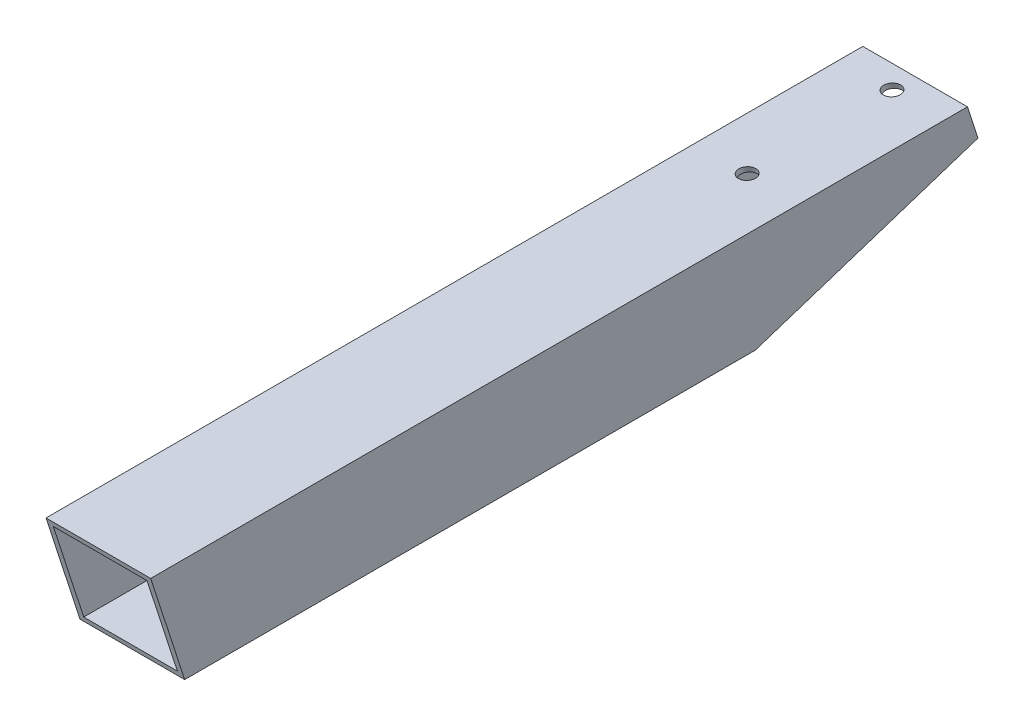
SolidWorks part; units mm, degrees
material "Gerais  - 6061-T6"
ref_plane "Plano frontal" through (0, 0, 0) normal (0, 0, 1) x (1, 0, 0)
ref_plane "Plano superior" through (0, 0, 0) normal (0, 1, 0) x (1, 0, 0)
ref_plane "Plano direito" through (0, 0, 0) normal (1, 0, 0) x (0, 0, -1)
sketch "Esboço1" plane through (0, 0, 0) normal (0, 0, 1) x (1, 0, 0)
  line L1 (-9.5, 9.5) -> (9.5, 9.5)
  line L2 (-9.5, 9.5) -> (-9.5, -9.5)
  line L3 (-9.5, -9.5) -> (9.5, -9.5)
  line L4 (9.5, 9.5) -> (9.5, -9.5)
  line L5 (-9.5, 9.5) -> (9.5, -9.5) construction
  line L6 (-9.5, -9.5) -> (9.5, 9.5) construction
  line L11 (-5.6574, 5.6574) -> (5.6574, -5.6574) construction
  line L12 (-5.6574, -5.6574) -> (5.6574, 5.6574) construction
  point P0 (0, 0)
  point P6 (0, 0)
  dimension "D1" = 19
extrude "Ressalto-extrusão1" add sketch "Esboço1" along normal blind 260
shell "Casca2" thickness 1
sketch "Esboço2" plane through (9.5, 0, 0) normal (1, 0, 0) x (0, 0, -1)
  line L0 (0, 9.5) -> (-58.476, -9.5)
  line L1 (-260, -9.5) -> (0, -9.5) construction
  line L4 (-260, 9.5) -> (0, 9.5) construction
  line L5 (-58.476, -9.5) -> (0, -9.5)
  line L7 (0, -9.5) -> (0, 9.5)
  dimension "D1" = 18
extrude "Corte-extrusão1" cut sketch "Esboço2" against normal through all
sketch "Esboço4" plane through (9.5, 0, 0) normal (1, 0, 0) x (0, 0, -1)
  line L0 (-168.5503, 10.4737) -> (-161.2895, -11.8728)
  line L1 (-161.2895, -11.8728) -> (-264.8128, -45.5096)
  line L2 (-264.8128, -45.5096) -> (-289.0578, 22.1497)
  line L3 (-289.0578, 22.1497) -> (-184.5161, 59.6112)
  line L4 (-184.5161, 59.6112) -> (-168.5503, 10.4737)
extrude "Corte-extrusão3" cut sketch "Esboço4" against normal through all
sketch "Esboço5" plane through (0, 9.5, 0) normal (0, 0.9511, 0.309) x (1, 0, 0)
  line L0 (9.5, 0) -> (-9.5, 0) construction
  line L1 (9.5, -160) -> (-9.5, -160) construction
  circle A0 centre (0, -23) radius 1.5
  circle A1 centre (0, -48) radius 1.5
  point P8 (0, 0)
  dimension "D3" = 3
  dimension "D1" = 112
  dimension "D2" = 25
extrude "Corte-extrusão4" cut sketch "Esboço5" along normal through all
sketch "Esboço7" plane through (0, 8.5928, 2.792) normal (0, -0.9511, -0.309) x (1, 0, 0)
  line L0 (-9.5, -2.9357) -> (-9.5, 58.5496) construction
  line L1 (9.5, -2.9357) -> (-9.5, -2.9357)
  line L2 (9.5, -2.9357) -> (9.5, 16.0643)
  line L3 (9.5, 16.0643) -> (-9.5, 16.0643)
  line L4 (-9.5, -2.9357) -> (-9.5, 16.0643)
  ellipse E0 centre (0, 20.0643) end of major axis (1.5, 20.0643) minor radius 1.5 construction
  point P7 (0, 20.0643)
  dimension "D1" = 4
extrude "Corte-extrusão6" cut sketch "Esboço7" against normal through all
